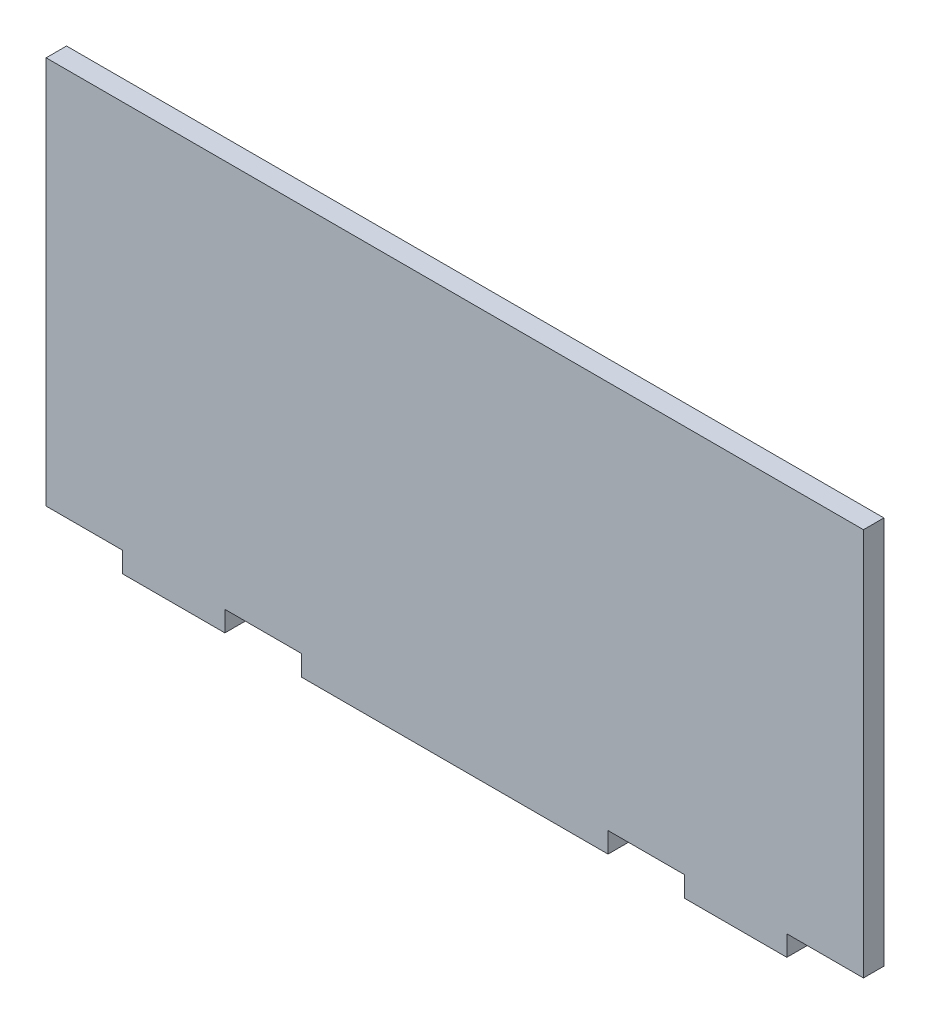
SolidWorks part; units mm, degrees
ref_plane "Front Plane" through (0, 0, 0) normal (0, 0, 1) x (1, 0, 0)
ref_plane "Top Plane" through (0, 0, 0) normal (0, 1, 0) x (1, 0, 0)
ref_plane "Right Plane" through (0, 0, 0) normal (1, 0, 0) x (0, 0, -1)
sketch "Sketch1" plane through (0, 0, 0) normal (0, 0, 1) x (1, 0, 0)
  line L1 (-101.6, 50.8) -> (101.6, 50.8)
  line L2 (-101.6, 50.8) -> (-101.6, -50.8)
  line L3 (-101.6, -50.8) -> (101.6, -50.8)
  line L4 (101.6, 50.8) -> (101.6, -50.8)
  line L5 (-101.6, 50.8) -> (101.6, -50.8) construction
  line L6 (-101.6, -50.8) -> (101.6, 50.8) construction
  point P0 (0, 0)
  dimension "D1" = 101.6
  dimension "D2" = 203.2
extrude "Boss-Extrude1" add sketch "Sketch1" along normal blind 5.08
sketch "Sketch2" plane through (0, 0, 5.08) normal (0, 0, 1) x (1, 0, 0)
  line L0 (-101.6, -50.8) -> (101.6, -50.8) construction
  line L1 (-101.6, -45.72) -> (-82.55, -45.72)
  line L2 (-101.6, -45.72) -> (-101.6, -50.8)
  line L3 (-101.6, -50.8) -> (-82.55, -50.8)
  line L4 (-82.55, -45.72) -> (-82.55, -50.8)
  line L5 (38.1, -45.72) -> (57.15, -45.72)
  line L6 (38.1, -45.72) -> (38.1, -50.8)
  line L7 (38.1, -50.8) -> (57.15, -50.8)
  line L8 (57.15, -45.72) -> (57.15, -50.8)
  line L9 (82.55, -45.72) -> (101.6, -45.72)
  line L10 (82.55, -45.72) -> (82.55, -50.8)
  line L11 (82.55, -50.8) -> (101.6, -50.8)
  line L12 (101.6, -45.72) -> (101.6, -50.8)
  line L13 (-101.6, 50.8) -> (-101.6, -50.8) construction
  line L14 (-57.15, -45.72) -> (-38.1, -45.72)
  line L15 (-57.15, -45.72) -> (-57.15, -50.8)
  line L16 (-57.15, -50.8) -> (-38.1, -50.8)
  line L17 (-38.1, -45.72) -> (-38.1, -50.8)
  line L18 (101.6, -50.8) -> (101.6, 50.8) construction
  dimension "D1" = 5.08
  dimension "D2" = 5.08
  dimension "D3" = 5.08
  dimension "D4" = 5.08
  dimension "D5" = 19.05
  dimension "D6" = 19.05
  dimension "D7" = 25.4
  dimension "D8" = 19.05
  dimension "D9" = 25.4
  dimension "D10" = 19.05
extrude "Cut-Extrude1" cut sketch "Sketch2" against normal up to surface (5.08 mm away) up to face at (0, 0, 0)
